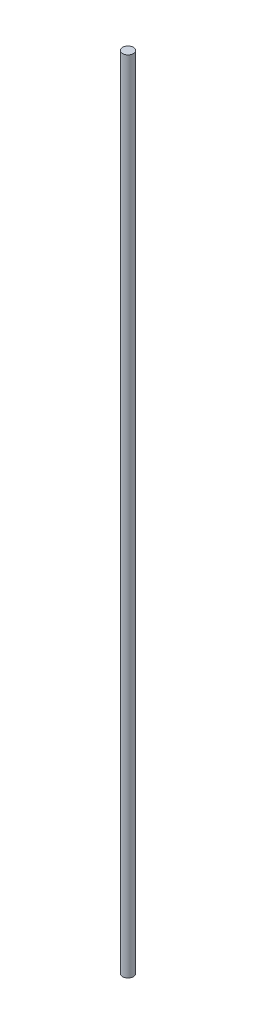
SolidWorks part; units mm, degrees
ref_plane "Front Plane" through (0, 0, 0) normal (0, 0, 1) x (1, 0, 0)
ref_plane "Top Plane" through (0, 0, 0) normal (0, 1, 0) x (1, 0, 0)
ref_plane "Right Plane" through (0, 0, 0) normal (1, 0, 0) x (0, 0, -1)
sketch "Sketch1" plane through (0, 0, 0) normal (0, 1, 0) x (1, 0, 0)
  circle A0 centre (0, 0) radius 1
  dimension "D1" = 2
extrude "Boss-Extrude1" add sketch "Sketch1" along normal blind 146.05
